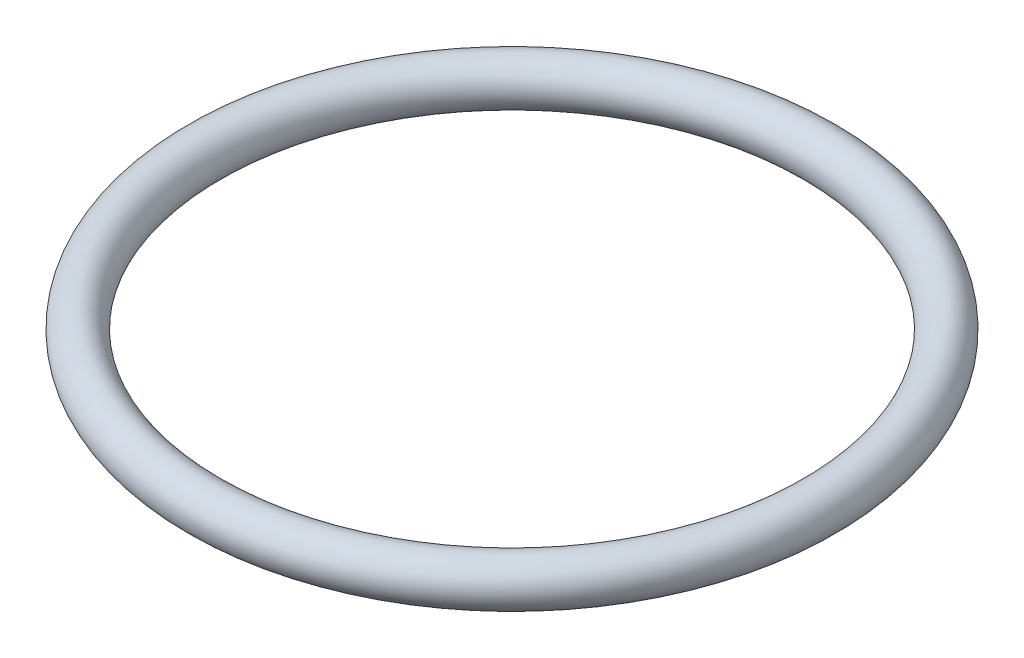
SolidWorks part; units mm, degrees
ref_plane "Front Plane" through (0, 0, 0) normal (0, 0, 1) x (1, 0, 0)
ref_plane "Top Plane" through (0, 0, 0) normal (0, 1, 0) x (1, 0, 0)
ref_plane "Right Plane" through (0, 0, 0) normal (1, 0, 0) x (0, 0, -1)
sketch "Sketch2" plane through (0, 0, 0) normal (0, 0, 1) x (1, 0, 0)
  line L0 (0, 0) -> (-11, 0) construction
  line L1 (0, 0) -> (0, 3.8206) construction
  circle A0 centre (-10.25, 0) radius 0.75
  point P3 (-10.25, 0)
  dimension "D1" = 11
  dimension "D2" = 0.75
revolve "Revolve1" add sketch "Sketch2" angle 360 about L1
sketch "Sketch3" plane through (0, 0, 0) normal (0, 1, 0) x (1, 0, 0)
  circle A0 centre (0, 0) radius 11
  dimension "D1" = 22
